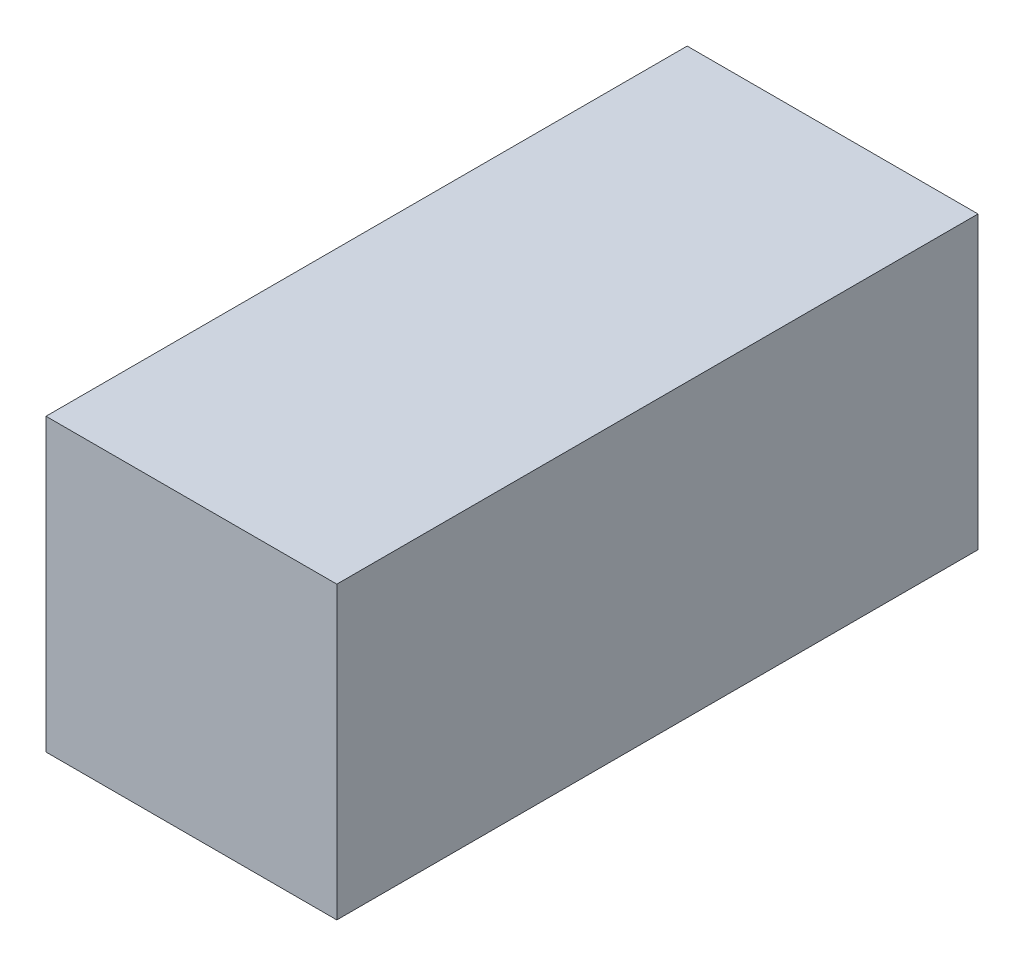
SolidWorks part; units mm, degrees
ref_plane "Alzado" through (0, 0, 0) normal (0, 0, 1) x (1, 0, 0)
ref_plane "Planta" through (0, 0, 0) normal (0, 1, 0) x (1, 0, 0)
ref_plane "Vista lateral" through (0, 0, 0) normal (1, 0, 0) x (0, 0, -1)
sketch "Croquis1" plane through (0, 0, 0) normal (0, 0, 1) x (1, 0, 0)
  line L0 (1.9, -1.9) -> (61.6, -1.9)
  line L1 (0, 0) -> (63.5, 0)
  line L2 (0, 0) -> (0, -63.5)
  line L3 (0, -63.5) -> (63.5, -63.5)
  line L4 (63.5, 0) -> (63.5, -63.5)
  line L5 (61.6, -1.9) -> (61.6, -61.6)
  line L6 (1.9, -61.6) -> (61.6, -61.6)
  line L7 (1.9, -1.9) -> (1.9, -61.6)
  dimension "D1" = 63.5
  dimension "D2" = 63.5
  dimension "D3" = 1.9
extrude "Saliente-Extruir1" add sketch "Croquis1" along normal blind 140
sketch "Croquis2" plane through (0, 0, 140) normal (0, 0, 1) x (1, 0, 0)
  line L1 (1.9, -1.9) -> (61.6, -1.9)
  line L2 (1.9, -1.9) -> (1.9, -61.6)
  line L3 (1.9, -61.6) -> (61.6, -61.6)
  line L4 (61.6, -1.9) -> (61.6, -61.6)
extrude "Saliente-Extruir2" add sketch "Croquis2" against normal blind 1.9
sketch "Croquis3" plane through (0, 0, 0) normal (0, 0, -1) x (-1, 0, 0)
  line L1 (-61.6, -1.9) -> (-1.9, -1.9)
  line L2 (-61.6, -1.9) -> (-61.6, -61.6)
  line L3 (-61.6, -61.6) -> (-1.9, -61.6)
  line L4 (-1.9, -1.9) -> (-1.9, -61.6)
extrude "Saliente-Extruir3" add sketch "Croquis3" against normal blind 1.9
